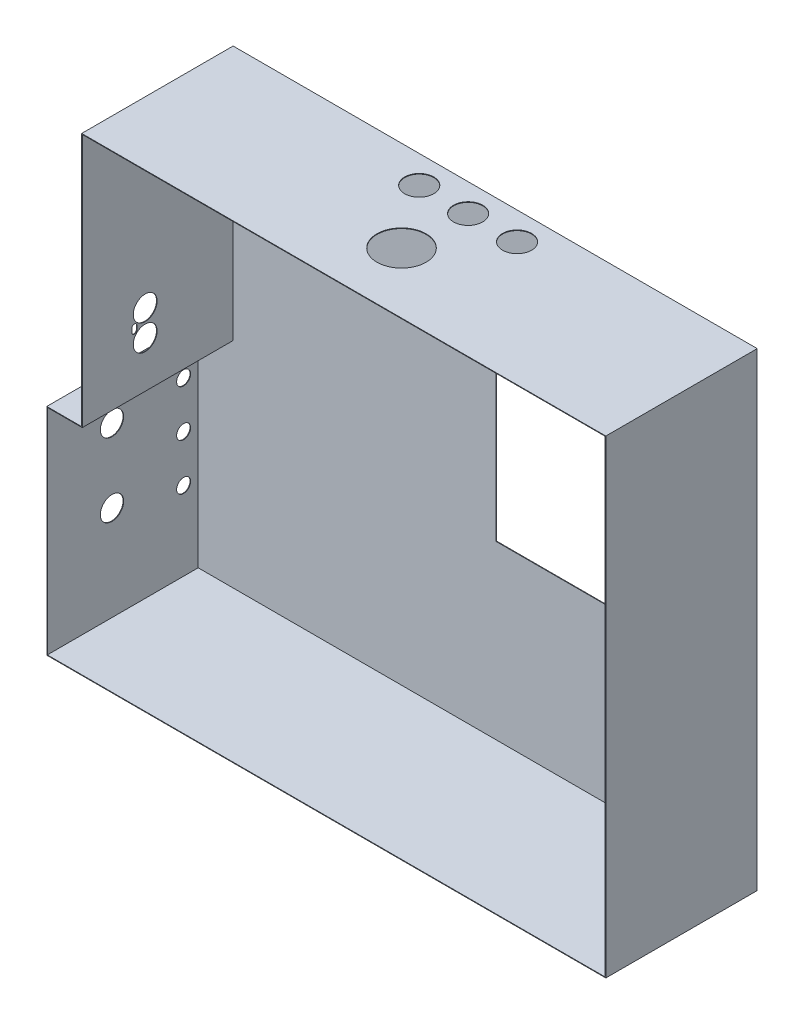
SolidWorks part; units mm, degrees
material "7075-O (SS)"
ref_plane "Płaszczyzna przednia" through (0, 0, 0) normal (0, 0, 1) x (1, 0, 0)
ref_plane "Płaszczyzna górna" through (0, 0, 0) normal (0, 1, 0) x (1, 0, 0)
ref_plane "Płaszczyzna prawa" through (0, 0, 0) normal (1, 0, 0) x (0, 0, -1)
sketch "Szkic1" plane through (0, 0, 0) normal (0, 0, 1) x (1, 0, 0)
  line L1 (0, 0) -> (450, 0)
  line L2 (0, 0) -> (0, 403)
  line L3 (0, 403) -> (450, 403)
  line L4 (450, 0) -> (450, 403)
  line L9 (0, 0) -> (-30, 0)
  line L10 (0, 0) -> (0, 185)
  line L11 (0, 185) -> (-30, 185)
  line L12 (-30, 0) -> (-30, 185)
  dimension "D1" = 403
  dimension "D2" = 450
  dimension "D3" = 30
  dimension "D4" = 185
extrude "Dodanie-wyciągnięcie1" add sketch "Szkic1" along normal blind 130
shell "Skorupa1" thickness 0.5
sketch "Szkic2" plane through (0, 0, 0) normal (0, 0, -1) x (-1, 0, 0)
  line L0 (-450, 0) -> (-450, 403) construction
  line L1 (-432, 280) -> (-226, 280)
  line L2 (-432, 280) -> (-432, 148)
  line L3 (-432, 148) -> (-226, 148)
  line L4 (-226, 280) -> (-226, 148)
  line L6 (30, 0) -> (-450, 0) construction
  dimension "D1" = 206
  dimension "D2" = 132
  dimension "D3" = 18
  dimension "D4" = 148
extrude "Wytnij-wyciągnięcie1" cut sketch "Szkic2" against normal up to next
sketch "Szkic4" plane through (0, 0, 0) normal (0, 0, -1) x (-1, 0, 0)
  line L0 (-114.4, 386.6) -> (-74.7, 386.6) construction
  line L1 (-74.7, 386.6) -> (-74.7, 365.2) construction
  line L2 (0, 403) -> (-450, 403) construction
  line L3 (0, 185) -> (0, 403) construction
  circle A0 centre (-114.4, 386.6) radius 2
  circle A2 centre (-74.7, 365.2) radius 2
  circle A3 centre (-74.7, 335.2) radius 2
  circle A4 centre (-114.4, 356.6) radius 2
  circle A5 centre (-74.7, 305.2) radius 2
  circle A6 centre (-114.4, 326.6) radius 2
  point P9 (-74.7, 334.3567)
  point P10 (-74.7, 330.3969)
  dimension "D4" = 4
  dimension "D5" = 4
  dimension "D6" = 74.7
  dimension "D1" = 39.7
  dimension "D2" = 21.4
  dimension "D3" = 16.4
  dimension "D8" = 30
  dimension "D7" = 3
extrude "Wytnij-wyciągnięcie2" cut sketch "Szkic4" against normal blind 10
sketch "Szkic5" plane through (0, 403, 0) normal (0, 1, 0) x (1, 0, 0)
  line L0 (267.5, -23.7) -> (183.5, -23.7) construction
  line L1 (0, -130) -> (0, 0) construction
  line L2 (0, 0) -> (450, 0) construction
  circle A0 centre (222.5, -77.9) radius 21.15
  circle A1 centre (225.5, -23.7) radius 12.5
  circle A2 centre (267.5, -23.7) radius 12.5
  circle A3 centre (183.5, -23.7) radius 12.5
  point P8 (0, 0)
  dimension "D1" = 3
  dimension "D3" = 25
  dimension "D6" = 42.3
  dimension "D2" = 183.5
  dimension "D4" = 23.7
  dimension "D5" = 42
  dimension "D7" = 54.2
extrude "Wytnij-wyciągnięcie3" cut sketch "Szkic5" against normal blind 10
sketch "Szkic6" plane through (-30, 0, 0) normal (-1, 0, 0) x (0, 0, 1)
  line L0 (13, 148) -> (13, 68) construction
  line L1 (74.5, 145) -> (74.5, 82) construction
  line L2 (0, 0) -> (0, 185) construction
  line L3 (130, 0) -> (0, 0) construction
  line L4 (130, 0) -> (130, 185) construction
  circle A0 centre (74.5, 145) radius 10
  circle A1 centre (74.5, 82) radius 10
  circle A2 centre (13, 148) radius 6
  circle A3 centre (13, 108) radius 6
  circle A4 centre (13, 68) radius 6
  dimension "D1" = 40
  dimension "D2" = 12
  dimension "D8" = 20
  dimension "D3" = 13
  dimension "D4" = 68
  dimension "D5" = 55.5
  dimension "D6" = 82
  dimension "D7" = 63
extrude "Wytnij-wyciągnięcie4" cut sketch "Szkic6" against normal blind 10
sketch "Szkic7" plane through (0.5, 0, 0) normal (1, 0, 0) x (0, 0, -1)
  line L0 (-76, 224.23) -> (-76, 246.58) construction
  line L1 (-76, 235.405) -> (-85.25, 235.405) construction
  line L2 (-85.25, 233.905) -> (-85.25, 236.905) construction
  line L3 (-87.5, 233.905) -> (-87.5, 236.905)
  line L4 (-83, 233.905) -> (-83, 236.905)
  line L5 (-130, 184.5) -> (-130, 402.5) construction
  line L6 (-130, 184.5) -> (-0.5, 184.5) construction
  arc A0 (-87.5, 233.905) -> (-83, 233.905) centre (-85.25, 233.905) ccw
  arc A1 (-83, 236.905) -> (-87.5, 236.905) centre (-85.25, 236.905) ccw
  circle A2 centre (-76, 224.23) radius 10.25
  circle A3 centre (-76, 246.58) radius 10.25
  point P6 (-85.25, 235.405)
  dimension "D3" = 22.35
  dimension "D5" = 20.5
  dimension "D1" = 3
  dimension "D2" = 4.5
  dimension "D4" = 7
  dimension "D6" = 54
  dimension "D7" = 39.73
extrude "Wytnij-wyciągnięcie5" cut sketch "Szkic7" against normal blind 10
